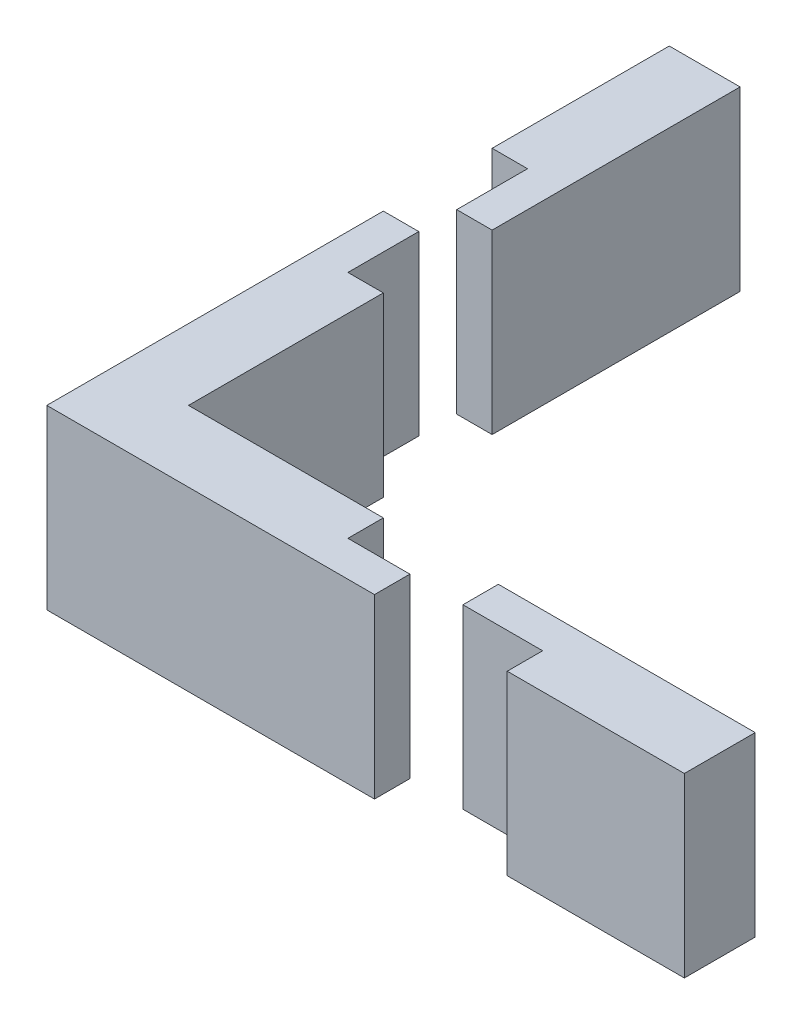
SolidWorks part; units mm, degrees
ref_plane "Front Plane" through (0, 0, 0) normal (0, 0, 1) x (1, 0, 0)
ref_plane "Top Plane" through (0, 0, 0) normal (0, 1, 0) x (1, 0, 0)
ref_plane "Right Plane" through (0, 0, 0) normal (1, 0, 0) x (0, 0, -1)
sketch "Sketch1" plane through (0, 0, 0) normal (0, 1, 0) x (1, 0, 0)
  line L1 (-2, 7.5) -> (2, 7.5)
  line L2 (-2, 7.5) -> (-2, -7.5)
  line L3 (-2, -7.5) -> (2, -7.5)
  line L4 (2, 7.5) -> (2, -7.5)
  line L5 (-2, 7.5) -> (2, -7.5) construction
  line L6 (-2, -7.5) -> (2, 7.5) construction
  line L7 (-2, 7.5) -> (0, 7.5)
  line L8 (-2, 7.5) -> (-2, 11.5)
  line L9 (-2, 11.5) -> (0, 11.5)
  line L10 (0, 7.5) -> (0, 11.5)
  line L11 (2, -7.5) -> (13, -7.5)
  line L12 (2, -7.5) -> (2, -3.5)
  line L13 (2, -3.5) -> (13, -3.5)
  line L14 (13, -7.5) -> (13, -3.5)
  line L15 (13, -7.5) -> (16.5, -7.5)
  line L16 (13, -7.5) -> (13, -5.5)
  line L17 (13, -5.5) -> (16.5, -5.5)
  line L18 (16.5, -7.5) -> (16.5, -5.5)
  line L19 (19.4949, -5.5) -> (23.9949, -5.5)
  line L20 (19.4949, -5.5) -> (19.4949, -3.5)
  line L21 (19.4949, -3.5) -> (23.9949, -3.5)
  line L22 (23.9949, -5.5) -> (23.9949, -3.5)
  line L23 (23.9949, -3.5) -> (33.9949, -3.5)
  line L24 (23.9949, -3.5) -> (23.9949, -7.5)
  line L25 (23.9949, -7.5) -> (33.9949, -7.5)
  line L26 (33.9949, -3.5) -> (33.9949, -7.5)
  line L27 (0, 13.6425) -> (2, 13.6425)
  line L28 (0, 13.6425) -> (0, 17.6425)
  line L29 (0, 17.6425) -> (2, 17.6425)
  line L30 (2, 13.6425) -> (2, 17.6425)
  line L31 (2, 17.6425) -> (-2, 17.6425)
  line L32 (2, 17.6425) -> (2, 27.6425)
  line L33 (2, 27.6425) -> (-2, 27.6425)
  line L34 (-2, 17.6425) -> (-2, 27.6425)
  point P0 (0, 0)
  dimension "D1" = 15
  dimension "D2" = 4
  dimension "D3" = 2
  dimension "D4" = 4
  dimension "D5" = 11
  dimension "D6" = 4
  dimension "D7" = 3.5
  dimension "D8" = 2
  dimension "D9" = 4.5
  dimension "D10" = 2
  dimension "D11" = 10
  dimension "D12" = 4
  dimension "D13" = 4
  dimension "D14" = 2
  dimension "D15" = 10
  dimension "D16" = 4
extrude "Boss-Extrude1" add sketch "Sketch1" along normal blind 10 contours L34 L31 L29 L32 L33 | L27 L30 L29 L28 | L1 L10 L9 L8 | L4 L1 L2 L3 | L11 L14 L13 L4 | L19 L22 L21 L20 | L15 L18 L17 L14 | L26 L23 L22 L24 L25
